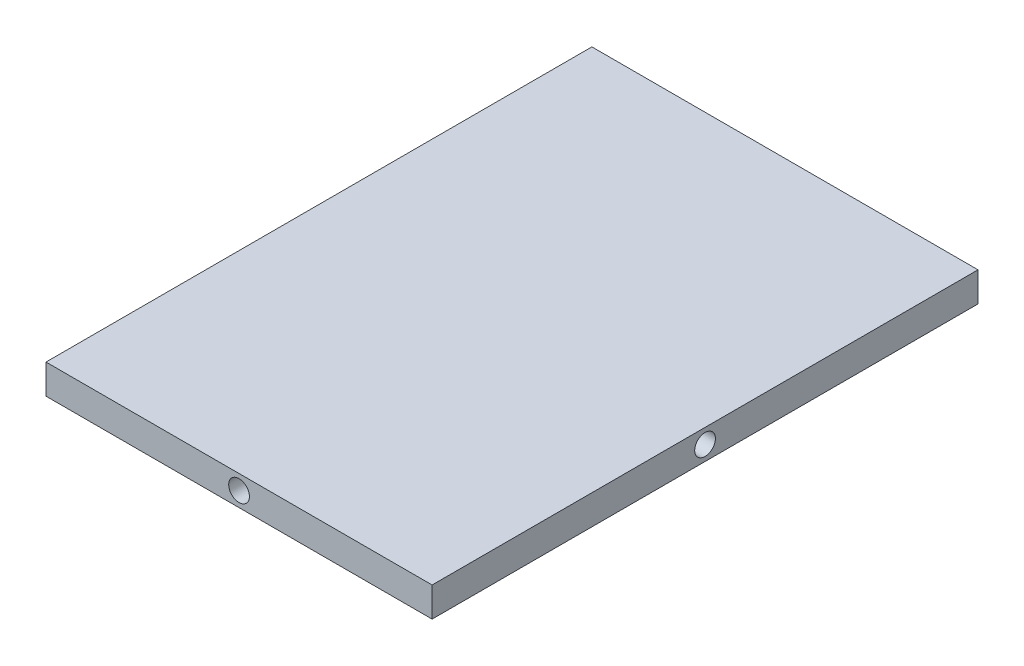
SolidWorks part; units mm, degrees
ref_plane "前视基准面" through (0, 0, 0) normal (0, 0, 1) x (1, 0, 0)
ref_plane "上视基准面" through (0, 0, 0) normal (0, 1, 0) x (1, 0, 0)
ref_plane "右视基准面" through (0, 0, 0) normal (1, 0, 0) x (0, 0, -1)
sketch "草图1" plane through (0, 0, 0) normal (0, 1, 0) x (1, 0, 0)
  line L1 (-65.25, -92.25) -> (65.25, -92.25)
  line L2 (-65.25, -92.25) -> (-65.25, 92.25)
  line L3 (-65.25, 92.25) -> (65.25, 92.25)
  line L4 (65.25, -92.25) -> (65.25, 92.25)
  line L5 (-65.25, -92.25) -> (65.25, 92.25) construction
  line L6 (-65.25, 92.25) -> (65.25, -92.25) construction
  point P0 (0, 0)
extrude "凸台-拉伸1" add sketch "草图1" along normal blind 10
sketch "草图2" plane through (0, 0, 92.25) normal (0, 0, 1) x (1, 0, 0)
  line L0 (-65.25, 10) -> (65.25, 0)
  line L1 (-65.25, 0) -> (65.25, 0) construction
  line L2 (65.25, 10) -> (65.25, 0) construction
  line L3 (65.25, 0) -> (65.25, 10)
  line L4 (65.25, 10) -> (-65.25, 0)
  circle A0 centre (0, 5) radius 3.5
extrude "切除-拉伸1" cut sketch "草图2" against normal blind 10 contours A0
sketch "草图3" plane through (65.25, 0, 0) normal (1, 0, 0) x (0, 0, -1)
  line L0 (-92.25, 10) -> (92.25, 0)
  line L1 (92.25, 0) -> (92.25, 10)
  line L2 (92.25, 10) -> (-92.25, 0)
  circle A0 centre (0, 5) radius 3.5
extrude "切除-拉伸2" cut sketch "草图3" against normal blind 10 contours A0
sketch "草图4" plane through (0, 0, -92.25) normal (0, 0, -1) x (-1, 0, 0)
  line L0 (-65.25, 10) -> (65.25, 0)
  line L1 (65.25, 0) -> (65.25, 10)
  line L2 (65.25, 10) -> (-65.25, 0)
  circle A0 centre (0, 5) radius 3.5
extrude "切除-拉伸3" cut sketch "草图4" against normal blind 10 contours L2 A0 L0 | L2 A0 L0 | L0 A0 L2 | L0 A0 L2
sketch "草图5" plane through (-65.25, 0, 0) normal (-1, 0, 0) x (0, 0, 1)
  line L0 (-92.25, 10) -> (92.25, 0)
  line L1 (92.25, 0) -> (92.25, 10)
  line L2 (92.25, 10) -> (-92.25, 0)
  circle A0 centre (0, 5) radius 3.5
extrude "切除-拉伸4" cut sketch "草图5" against normal blind 10 contours A0
